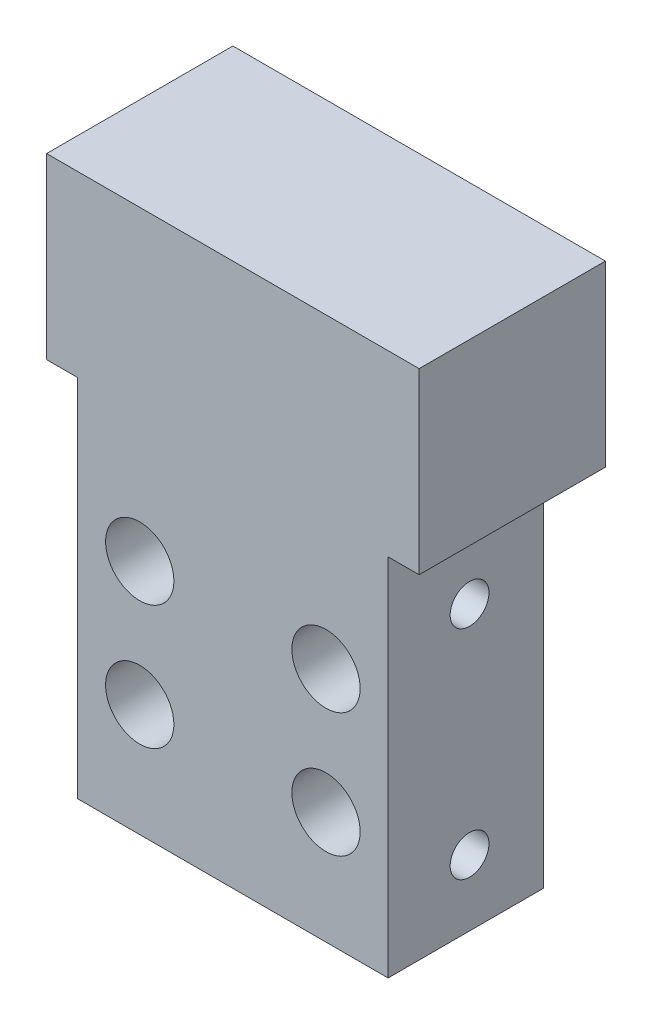
SolidWorks part; units mm, degrees
ref_plane "Front Plane" through (0, 0, 0) normal (0, 0, 1) x (1, 0, 0)
ref_plane "Top Plane" through (0, 0, 0) normal (0, 1, 0) x (1, 0, 0)
ref_plane "Right Plane" through (0, 0, 0) normal (1, 0, 0) x (0, 0, -1)
sketch "Sketch1" plane through (0, 0, 0) normal (0, 0, 1) x (1, 0, 0)
  line L1 (0, 0) -> (20, 0)
  line L2 (0, 0) -> (0, 22.5)
  line L3 (0, 22.5) -> (20, 22.5)
  line L4 (20, 0) -> (20, 22.5)
  dimension "D1" = 20
  dimension "D2" = 22.5
extrude "Boss-Extrude1" add sketch "Sketch1" along normal blind 10
hole_wizard "CBORE for M2 SHCS1" positions "Sketch2" profile "Sketch3" counterbore size "M2" standard "ANSI Metric" end condition through all
sketch "Sketch2" plane through (0, 0, 10) normal (0, 0, 1) x (1, 0, 0)
  line L0 (0, 22.5) -> (0, 0) construction
  line L1 (20, 22.5) -> (0, 22.5) construction
  point P0 (4, 15.25)
  point P11 (16, 15.25)
  point P12 (16, 7.25)
  point P13 (4, 7.25)
  dimension "D1" = 4
  dimension "D4" = 7.25
  dimension "D2" = 2
  dimension "D3" = 2
sketch "Sketch3" plane through (4, 15.25, 10) normal (1, 0, 0) x (0, -1, 0)
  line L0 (0, 0) -> (0, 10)
  line L1 (0, 10) -> (1.2, 10)
  line L3 (1.2, 10) -> (1.2, 4)
  line L4 (1.2, 4) -> (2.2, 4)
  line L5 (2.2, 4) -> (2.2, 0)
  line L7 (2.2, 0) -> (0, 0)
  line L11 (0, -6.35) -> (0, 107.95) construction
  dimension "Thru Hole Dia." = 2.4
  dimension "Thru Hole Depth" = 10
  dimension "C'Bore Dia." = 4.4
  dimension "C'Bore Depth" = 4
sketch "Sketch4" plane through (0, 22.5, 0) normal (0, 1, 0) x (1, 0, 0)
  line L0 (20, -10) -> (20, 0) construction
  line L1 (22, 2) -> (-2, 2)
  line L2 (22, 2) -> (22, -10)
  line L3 (22, -10) -> (-2, -10)
  line L4 (-2, 2) -> (-2, -10)
  line L5 (20, 0) -> (0, 0) construction
  line L6 (20, -10) -> (0, -10) construction
  dimension "D2" = 24
  dimension "D3" = 2
  dimension "D4" = 2
extrude "Boss-Extrude2" add sketch "Sketch4" along normal blind 12.5
hole_wizard "Tap Drill for M3x0.5 Tap1" positions "Sketch5" profile "Sketch6" hole size "M3x0.5" standard "ANSI Metric"
sketch "Sketch5" plane through (20, 0, 0) normal (1, 0, 0) x (0, 0, -1)
  point P0 (-4.7518, 18.25)
  point P3 (-4.7518, 4.25)
sketch "Sketch6" plane through (20, 18.25, 4.7518) normal (0, 1, 0) x (0, 0, -1)
  line L0 (0, 0) -> (0, 4.7511)
  line L1 (0, 4.7511) -> (1.25, 4)
  line L2 (1.25, 4) -> (1.25, 0)
  line L5 (1.25, 0) -> (0, 0)
  line L10 (0, 4.7511) -> (-1.25, 4) construction
  line L11 (0, -6.35) -> (0, 107.95) construction
  dimension "Hole Dia." = 2.5
  dimension "Hole Depth" = 4
  dimension "Drill Angle" = 118
hole_wizard "Tap Drill for M3x0.5 Tap2" positions "Sketch7" profile "Sketch8" hole size "M3x0.5" standard "ANSI Metric"
sketch "Sketch7" plane through (0, 0, 0) normal (-1, 0, 0) x (0, 0, 1)
  point P0 (4.7518, 18.25)
  point P3 (4.7518, 4.25)
sketch "Sketch8" plane through (0, 18.25, 4.7518) normal (0, 1, 0) x (0, 0, 1)
  line L0 (0, 0) -> (0, 4.7511)
  line L1 (0, 4.7511) -> (1.25, 4)
  line L2 (1.25, 4) -> (1.25, 0)
  line L5 (1.25, 0) -> (0, 0)
  line L10 (0, 4.7511) -> (-1.25, 4) construction
  line L11 (0, -6.35) -> (0, 107.95) construction
  dimension "Hole Dia." = 2.5
  dimension "Hole Depth" = 4
  dimension "Drill Angle" = 118
sketch "Sketch9" plane through (0, 22.5, 0) normal (0, -1, 0) x (1, 0, 0)
  line L8 (0, 0) -> (0, 10)
  line L9 (0, 10) -> (-2, 10)
  line L10 (-2, 10) -> (-2, -2)
  line L11 (-2, -2) -> (22, -2)
  line L12 (22, -2) -> (22, 10)
  line L13 (22, 10) -> (20, 10)
  line L14 (20, 10) -> (20, 0)
  line L15 (20, 0) -> (0, 0)
  line L16 (0, 0) -> (0, 10)
  line L17 (0, 10) -> (-2, 10)
  line L18 (-2, 10) -> (-2, -2)
  line L19 (-2, -2) -> (22, -2)
  line L20 (22, -2) -> (22, 10)
  line L21 (22, 10) -> (20, 10)
  line L22 (20, 10) -> (20, 0)
  line L23 (20, 0) -> (0, 0)
  dimension "D1" = 0
extrude "Cut-Extrude1" cut sketch "Sketch9" against normal blind 1
